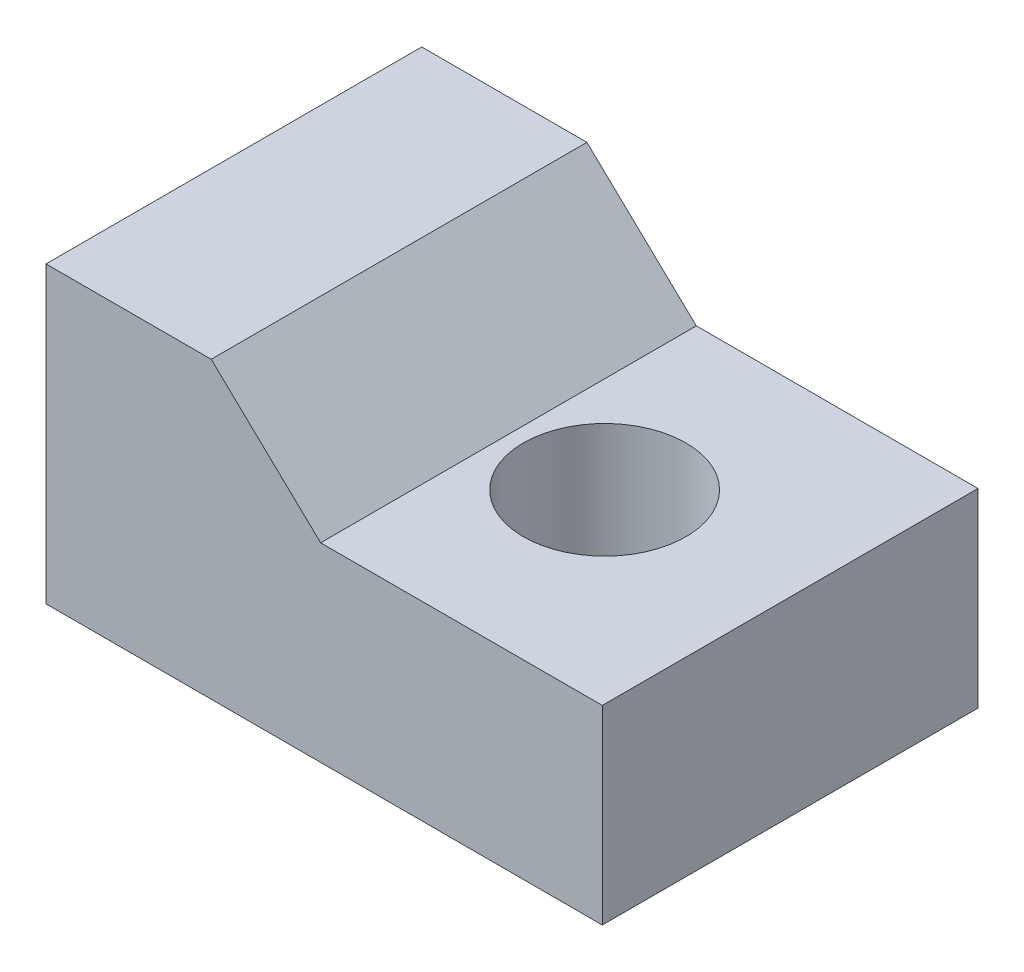
SolidWorks part; units mm, degrees
ref_plane "Front Plane" through (0, 0, 0) normal (0, 0, 1) x (1, 0, 0)
ref_plane "Top Plane" through (0, 0, 0) normal (0, 1, 0) x (1, 0, 0)
ref_plane "Right Plane" through (0, 0, 0) normal (1, 0, 0) x (0, 0, -1)
sketch "Sketch1" plane through (0, 0, 0) normal (0, 0, 1) x (1, 0, 0)
  line L0 (0, 0) -> (0, 14.351)
  line L1 (0, 14.351) -> (8.0518, 14.351)
  line L2 (8.0518, 14.351) -> (13.3858, 9.271)
  line L3 (13.3858, 9.271) -> (27.1145, 9.271)
  line L4 (27.1145, 9.271) -> (27.1145, 0)
  line L5 (27.1145, 0) -> (0, 0)
  dimension "D1" = 14.351
  dimension "D2" = 8.0518
  dimension "D3" = 9.271
  dimension "D4" = 5.334
  dimension "D5" = 27.1145
extrude "Boss-Extrude1" add sketch "Sketch1" along normal blind 18.3134
sketch "Sketch2" plane through (0, 9.271, 0) normal (0, 1, 0) x (1, 0, 0)
  line L0 (27.1145, 0) -> (13.3858, 0) construction
  line L1 (27.1145, -18.3134) -> (27.1145, 0) construction
  circle A0 centre (18.0721, -9.1567) radius 3.9624
  dimension "D1" = 7.9248
  dimension "D2" = 9.1567
  dimension "D3" = 9.0424
extrude "Cut-Extrude1" cut sketch "Sketch2" against normal through all
sketch "Sketch3" plane through (0, 0, 0) normal (-1, 0, 0) x (0, 0, 1)
  line L0 (18.3134, 0) -> (0, 0) construction
  circle A0 centre (9.1567, 6.096) radius 3.81
  dimension "D1" = 7.62
  dimension "D2" = 6.096
extrude "Cut-Extrude2" cut sketch "Sketch3" against normal blind 6.35
